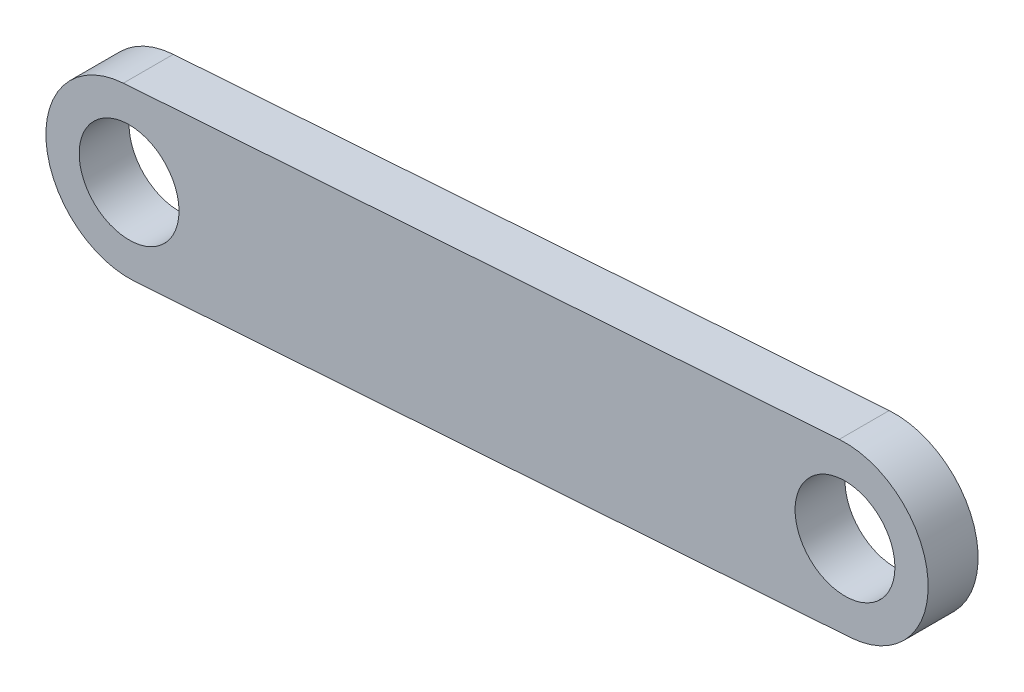
SolidWorks part; units mm, degrees
ref_plane "Front Plane" through (0, 0, 0) normal (0, 0, 1) x (1, 0, 0)
ref_plane "Top Plane" through (0, 0, 0) normal (0, 1, 0) x (1, 0, 0)
ref_plane "Right Plane" through (0, 0, 0) normal (1, 0, 0) x (0, 0, -1)
sketch "Sketch2" plane through (0, 0, 0) normal (0, 0, 1) x (1, 0, 0)
  line L0 (0, 0) -> (109.277, 7.5497) construction
  line L1 (-0.8753, 12.6698) -> (108.4017, 20.2195)
  line L2 (0.8753, -12.6698) -> (110.1523, -5.1201)
  arc A0 (-0.8753, 12.6698) -> (0.8753, -12.6698) centre (0, 0) ccw
  arc A1 (110.1523, -5.1201) -> (108.4017, 20.2195) centre (109.277, 7.5497) ccw
  circle A2 centre (0, 0) radius 7.62
  circle A3 centre (109.277, 7.5497) radius 7.62
  point P3 (54.6385, 3.7748)
extrude "Boss-Extrude1" add sketch "Sketch2" along normal blind 7.62
